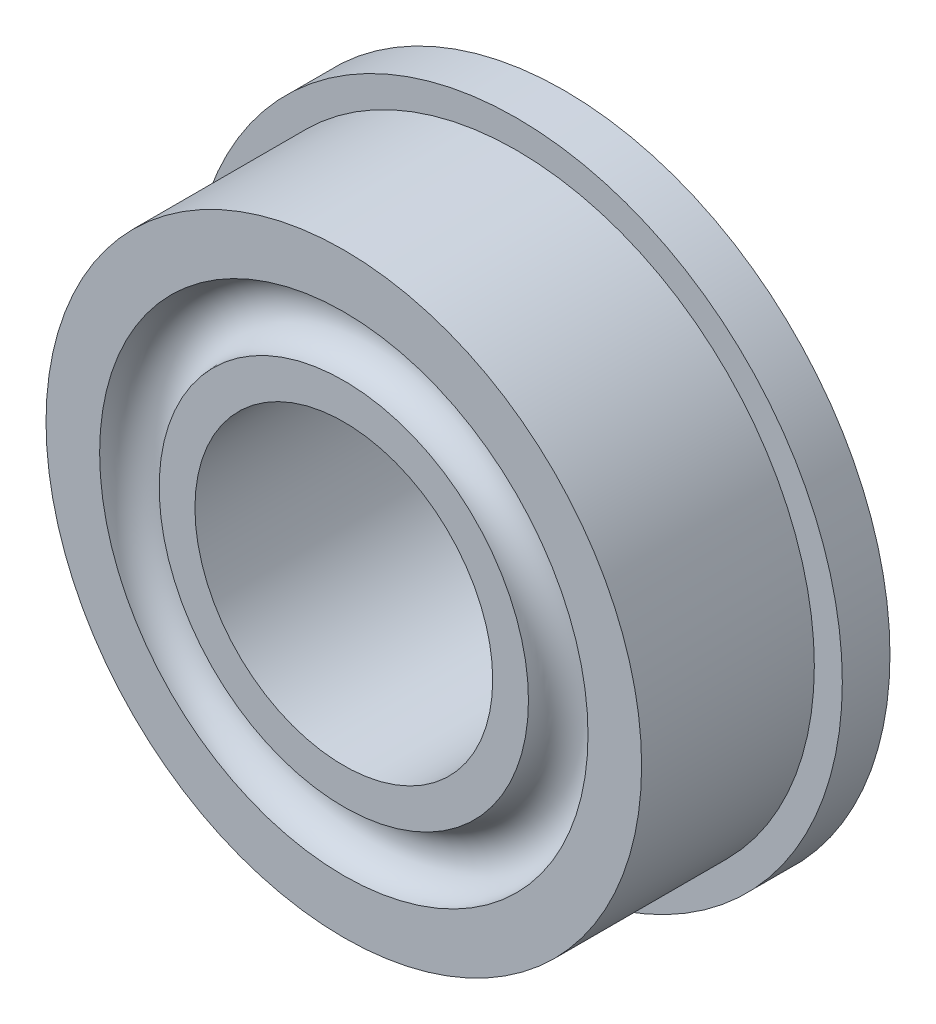
SolidWorks part; units mm, degrees
ref_plane "Front Plane" through (0, 0, 0) normal (0, 0, 1) x (1, 0, 0)
ref_plane "Top Plane" through (0, 0, 0) normal (0, 1, 0) x (1, 0, 0)
ref_plane "Right Plane" through (0, 0, 0) normal (1, 0, 0) x (0, 0, -1)
sketch "Sketch1" plane through (0, 0, 0) normal (0, 0, 1) x (1, 0, 0)
  circle A0 centre (0, 0) radius 6.9469
  circle A1 centre (0, 0) radius 3.175
  dimension "D1" = 13.8938
  dimension "D2" = 6.35
extrude "Boss-Extrude1" add sketch "Sketch1" along normal blind 1.016
sketch "Sketch2" plane through (0, 0, 1.016) normal (0, 0, 1) x (1, 0, 0)
  circle A0 centre (0, 0) radius 3.175
  circle A1 centre (0, 0) radius 6.35
  dimension "D1" = 6.35
  dimension "D2" = 12.7
extrude "Boss-Extrude2" add sketch "Sketch2" along normal blind 3.683
ref_axis "Axis1" through (0, 0, 4.699) along (0, 0, -1)
sketch "Sketch7" plane through (0, 0, 0) normal (1, 0, 0) x (0, 0, -1)
  line L0 (-4.699, 6.35) -> (-4.699, -6.35) construction
  line L1 (-4.699, 0) -> (0, 0) construction
  line L2 (-4.699, 5.207) -> (-4.699, 3.937)
  line L3 (0, -6.9469) -> (0, 6.9469) construction
  line L4 (0, 5.207) -> (0, 3.937)
  arc A0 (-4.699, 5.207) -> (-4.699, 3.937) centre (-4.699, 4.572) cw
  arc A1 (0, 5.207) -> (0, 3.937) centre (0, 4.572) ccw
  dimension "D1" = 0.635
  dimension "D3" = 0.635
  dimension "D2" = 4.572
  dimension "D4" = 4.572
revolve "Cut-Revolve2" cut sketch "Sketch7" angle 360 about axis through (0, 0, 4.699) along (0, 0, -1)
